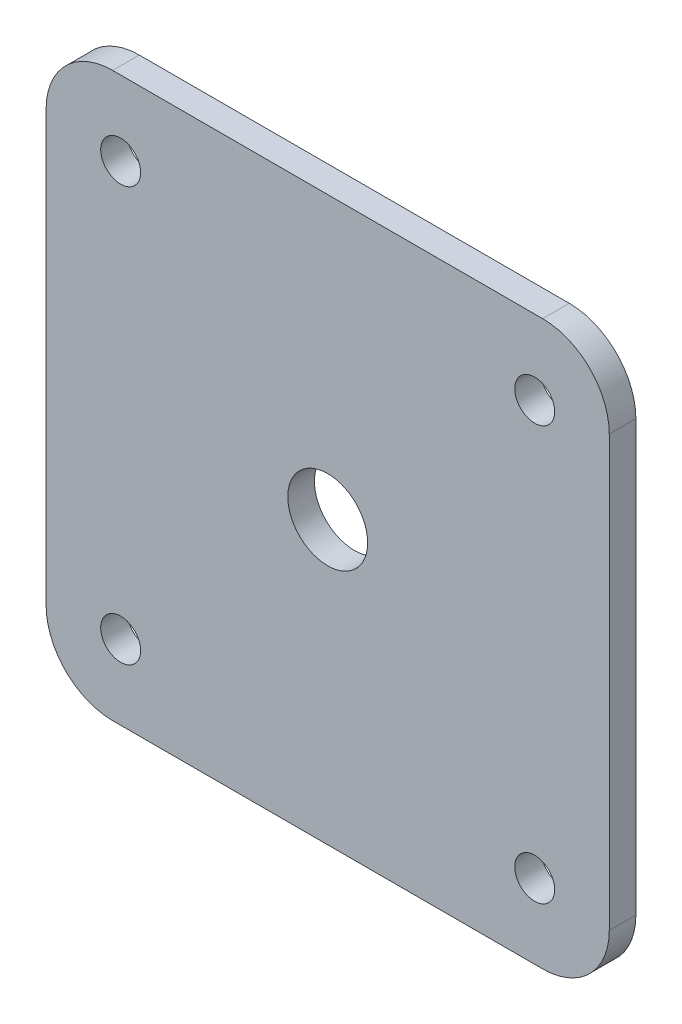
SolidWorks part; units mm, degrees
ref_plane "Front" through (0, 0, 0) normal (0, 0, 1) x (1, 0, 0)
ref_plane "Top" through (0, 0, 0) normal (0, 1, 0) x (1, 0, 0)
ref_plane "Right" through (0, 0, 0) normal (1, 0, 0) x (0, 0, -1)
sketch "Sketch1" plane through (0, 0, 0) normal (0, 0, 1) x (1, 0, 0)
  line L1 (-16.15, -21.15) -> (16.15, -21.15)
  line L2 (-21.15, -16.15) -> (-21.15, 16.15)
  line L3 (-16.15, 21.15) -> (16.15, 21.15)
  line L4 (21.15, -16.15) -> (21.15, 16.15)
  line L5 (-21.15, -21.15) -> (21.15, 21.15) construction
  line L6 (-21.15, 21.15) -> (21.15, -21.15) construction
  line L7 (-15.55, -15.55) -> (15.55, -15.55) construction
  line L8 (-15.55, -15.55) -> (-15.55, 15.55) construction
  line L9 (-15.55, 15.55) -> (15.55, 15.55) construction
  line L10 (15.55, -15.55) -> (15.55, 15.55) construction
  line L11 (-15.55, -15.55) -> (15.55, 15.55) construction
  line L12 (-15.55, 15.55) -> (15.55, -15.55) construction
  circle A0 centre (-15.55, 15.55) radius 1.5
  circle A1 centre (15.55, 15.55) radius 1.5
  circle A2 centre (15.55, -15.55) radius 1.5
  circle A3 centre (-15.55, -15.55) radius 1.5
  arc A4 (16.15, 21.15) -> (21.15, 16.15) centre (16.15, 16.15) cw
  arc A5 (16.15, -21.15) -> (21.15, -16.15) centre (16.15, -16.15) ccw
  arc A6 (-21.15, -16.15) -> (-16.15, -21.15) centre (-16.15, -16.15) ccw
  arc A7 (-21.15, 16.15) -> (-16.15, 21.15) centre (-16.15, 16.15) cw
  circle A8 centre (0, 0) radius 3
  point P0 (0, 0)
  point P6 (0, 0)
  dimension "D1" = 3
  dimension "D4" = 5
  dimension "D5" = 6
  dimension "D2" = 42.3
  dimension "D3" = 31.1
extrude "Boss-Extrude1" add sketch "Sketch1" along normal blind 2
